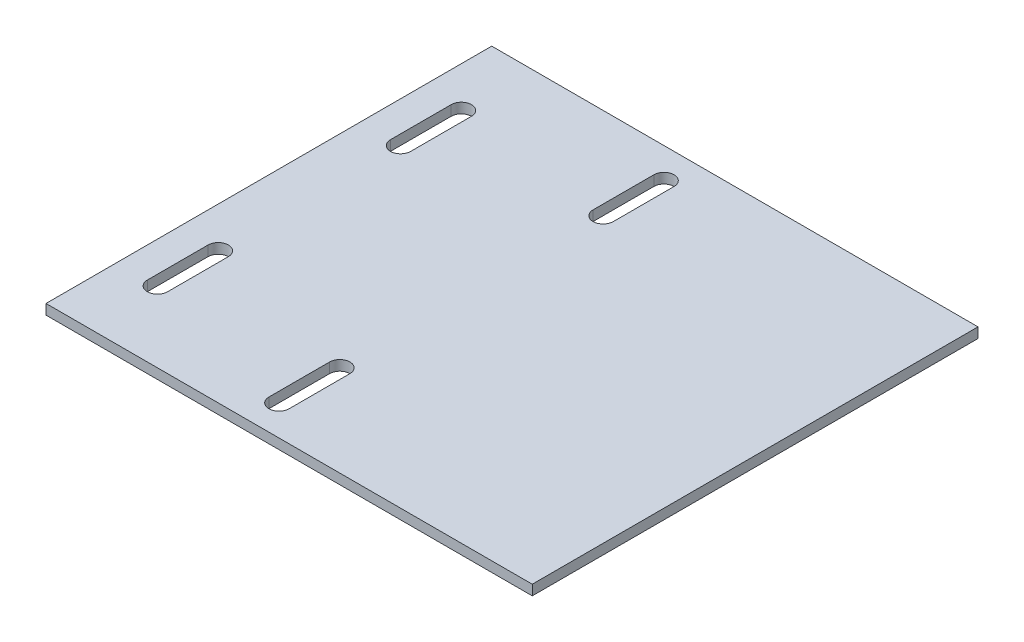
SolidWorks part; units mm, degrees
material "ASTM A36 Steel"
ref_plane "Front Plane" through (0, 0, 0) normal (0, 0, 1) x (1, 0, 0)
ref_plane "Top Plane" through (0, 0, 0) normal (0, 1, 0) x (1, 0, 0)
ref_plane "Right Plane" through (0, 0, 0) normal (1, 0, 0) x (0, 0, -1)
sketch "Sketch1" plane through (0, 0, 0) normal (0, 1, 0) x (1, 0, 0)
  line L1 (76.2, 69.85) -> (-76.2, 69.85)
  line L2 (76.2, 69.85) -> (76.2, -69.85)
  line L3 (76.2, -69.85) -> (-76.2, -69.85)
  line L4 (-76.2, 69.85) -> (-76.2, -69.85)
  line L5 (76.2, 69.85) -> (-76.2, -69.85) construction
  line L6 (76.2, -69.85) -> (-76.2, 69.85) construction
  point P0 (0, 0)
  dimension "D1" = 139.7
  dimension "D2" = 152.4
extrude "Boss-Extrude1" add sketch "Sketch1" along normal blind 3.175
sketch "Sketch2" plane through (0, 3.175, 0) normal (0, 1, 0) x (1, 0, 0)
  line L0 (-76.2, 69.85) -> (-76.2, -69.85) construction
  line L1 (-2.6194, 0) -> (2.6194, 0) construction
  line L6 (-63.5, -38.1) -> (-63.5, 38.1) construction
  line L8 (-12.7, -50.8) -> (-12.7, 50.8) construction
  line L9 (-63.5, -38.1) -> (-12.7, 50.8) construction
  line L10 (-63.5, 38.1) -> (-12.7, -50.8) construction
  line L12 (-12.7, -41.275) -> (-12.7, -60.325) construction
  line L13 (-9.525, -41.275) -> (-9.525, -60.325)
  line L14 (-15.875, -41.275) -> (-15.875, -60.325)
  line L15 (-12.7, 41.275) -> (-12.7, 60.325) construction
  line L16 (-15.875, 41.275) -> (-15.875, 60.325)
  line L17 (-9.525, 41.275) -> (-9.525, 60.325)
  line L18 (-63.5, -28.575) -> (-63.5, -47.625) construction
  line L19 (-60.325, -28.575) -> (-60.325, -47.625)
  line L20 (-66.675, -28.575) -> (-66.675, -47.625)
  line L21 (-63.5, 47.625) -> (-63.5, 28.575) construction
  line L22 (-60.325, 47.625) -> (-60.325, 28.575)
  line L23 (-66.675, 47.625) -> (-66.675, 28.575)
  arc A0 (-9.525, -41.275) -> (-15.875, -41.275) centre (-12.7, -41.275) ccw
  arc A1 (-15.875, -60.325) -> (-9.525, -60.325) centre (-12.7, -60.325) ccw
  arc A2 (-15.875, 41.275) -> (-9.525, 41.275) centre (-12.7, 41.275) ccw
  arc A3 (-9.525, 60.325) -> (-15.875, 60.325) centre (-12.7, 60.325) ccw
  arc A4 (-60.325, -28.575) -> (-66.675, -28.575) centre (-63.5, -28.575) ccw
  arc A5 (-66.675, -47.625) -> (-60.325, -47.625) centre (-63.5, -47.625) ccw
  arc A6 (-60.325, 47.625) -> (-66.675, 47.625) centre (-63.5, 47.625) ccw
  arc A7 (-66.675, 28.575) -> (-60.325, 28.575) centre (-63.5, 28.575) ccw
  point P0 (-41.7286, 0)
  point P7 (-63.5, 0)
  point P11 (-12.7, -50.8)
  point P18 (-12.7, 50.8)
  point P27 (-63.5, -38.1)
  point P34 (-63.5, 38.1)
  dimension "D1" = 63.5
  dimension "D2" = 101.6
  dimension "D3" = 19.05
  dimension "D4" = 6.35
  dimension "D5" = 50.8
  dimension "D6" = 76.2
extrude "Cut-Extrude1" cut sketch "Sketch2" against normal through all contours L14 A1 L13 A0 | L17 A3 L16 A2 | L20 A5 L19 A4 | L23 A7 L22 A6
